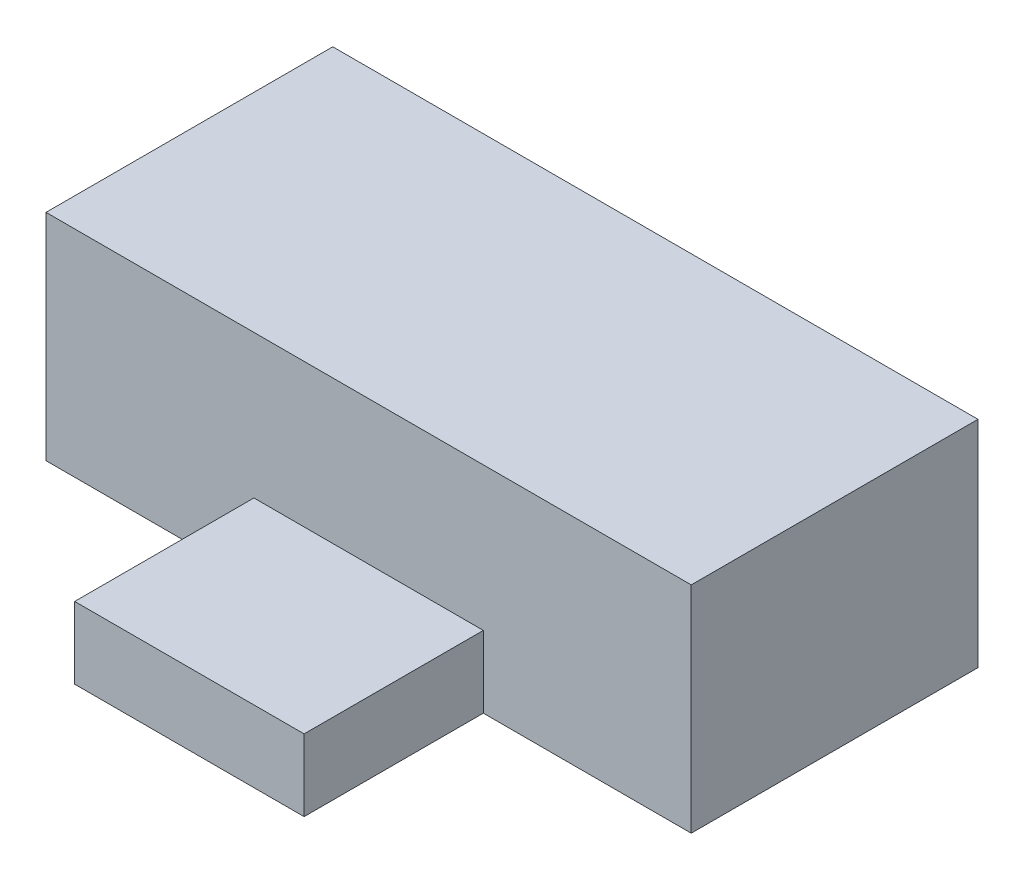
SolidWorks part; units mm, degrees
ref_plane "Plan de face" through (0, 0, 0) normal (0, 0, 1) x (1, 0, 0)
ref_plane "Plan de dessus" through (0, 0, 0) normal (0, 1, 0) x (1, 0, 0)
ref_plane "Plan de droite" through (0, 0, 0) normal (1, 0, 0) x (0, 0, -1)
sketch "Esquisse1" plane through (0, 0, 0) normal (0, 1, 0) x (1, 0, 0)
  line L1 (-9, 4) -> (9, 4)
  line L2 (-9, 4) -> (-9, -4)
  line L3 (-9, -4) -> (9, -4)
  line L4 (9, 4) -> (9, -4)
  line L5 (-9, 4) -> (9, -4) construction
  line L6 (-9, -4) -> (9, 4) construction
  point P0 (0, 0)
  dimension "D1" = 18
  dimension "D2" = 8
extrude "Boss.-Extru.1" add sketch "Esquisse1" along normal blind 6
sketch "Esquisse2" plane through (0, 0, 4) normal (0, 0, 1) x (1, 0, 0)
  line L0 (0, 1) -> (0, 0) construction
  line L1 (-3.2, 2) -> (3.2, 2)
  line L2 (-3.2, 2) -> (-3.2, 0)
  line L3 (-3.2, 0) -> (3.2, 0)
  line L4 (3.2, 2) -> (3.2, 0)
  line L5 (-3.2, 2) -> (3.2, 0) construction
  line L6 (-3.2, 0) -> (3.2, 2) construction
  line L7 (-9, 0) -> (9, 0) construction
  point P0 (0, 1)
  dimension "D1" = 2
  dimension "D2" = 6.4
extrude "Boss.-Extru.2" add sketch "Esquisse2" along normal blind 5
